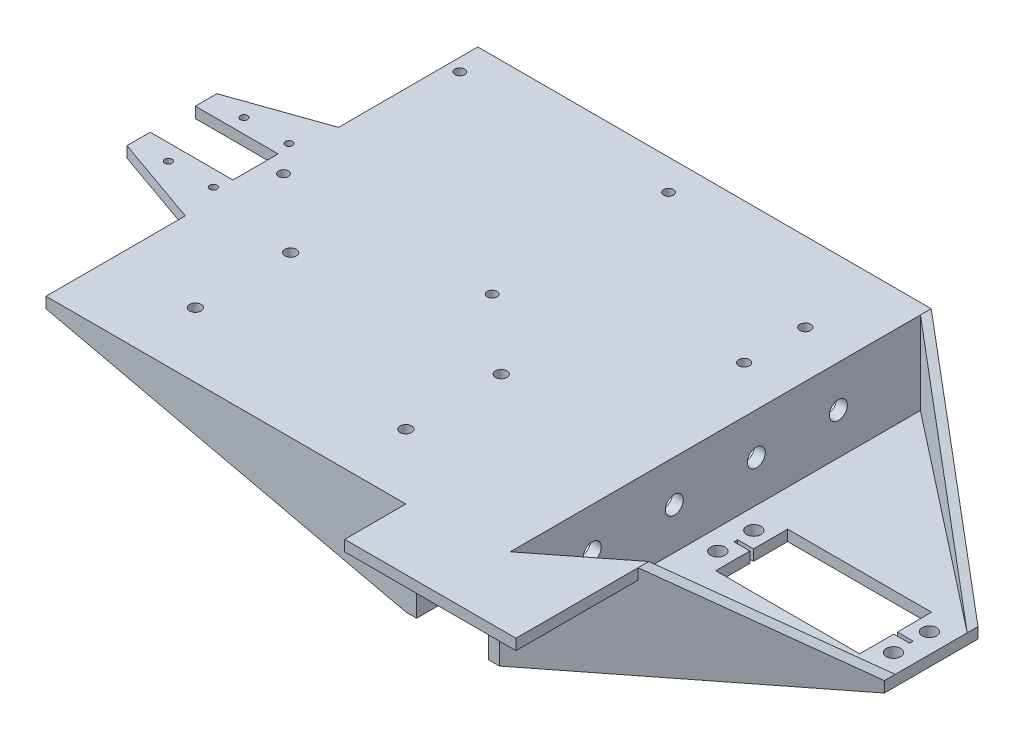
SolidWorks part; units mm, degrees
ref_plane "Front Plane" through (0, 0, 0) normal (0, 0, 1) x (1, 0, 0)
ref_plane "Top Plane" through (0, 0, 0) normal (0, 1, 0) x (1, 0, 0)
ref_plane "Right Plane" through (0, 0, 0) normal (1, 0, 0) x (0, 0, -1)
sketch "Sketch1" plane through (0, 0, 0) normal (0, 0, 1) x (1, 0, 0)
  line L0 (0, 0) -> (20, 0)
  line L1 (20, 0) -> (20, -23)
  line L2 (0, 0) -> (0, -23)
  line L3 (0, -23) -> (-103, -23)
  line L4 (-103, -23) -> (-103, -20)
  line L5 (-103, -20) -> (-3, -20)
  line L6 (-3, -20) -> (-3, 3)
  line L7 (-3, 3) -> (23, 3)
  line L8 (23, 3) -> (23, -20)
  line L9 (23, -20) -> (83, -20)
  line L10 (83, -20) -> (83, -23)
  line L11 (83, -23) -> (20, -23)
extrude "Boss-Extrude1" add sketch "Sketch1" along normal blind 120
sketch "Sketch2" plane through (0, 0, 0) normal (0, 0, -1) x (-1, 0, 0)
  line L0 (-23, 3) -> (3, 3) construction
  line L1 (-10, 3) -> (-10, 18)
  line L2 (-10, 18) -> (103, -20)
  line L3 (103, -20) -> (3, -20)
  line L4 (3, -20) -> (3, 3)
  line L5 (3, 3) -> (-10, 3)
  line L6 (-10, 18) -> (-10, 3)
  line L7 (-23, 3) -> (-23, -20)
  line L8 (-23, -20) -> (-83, -20)
  line L9 (-83, -20) -> (-10, 18)
  line L10 (-23, 3) -> (-10, 3)
  line L11 (3, 3) -> (3, 13.6283)
  line L12 (3, 13.6283) -> (-18.3982, 13.6283)
  line M4 (103, -20) -> (3, -20)
  line M5 (3, -20) -> (3, 3)
  line M6 (3, 3) -> (-23, 3)
  line M7 (-23, 3) -> (-23, -20)
  line M8 (-23, -20) -> (-83, -20)
extrude "Boss-Extrude2" add sketch "Sketch2" against normal blind 3 contours L11 L12 L1 M6 | L1 L12 L9 M8 M7 M6 | L11 L2 M5 M4
sketch "Sketch4" plane through (0, 0, 120) normal (0, 0, 1) x (1, 0, 0)
  line L0 (83, -20) -> (23, -20)
  line L1 (23, -20) -> (23, 3)
  line L2 (23, 3) -> (-3, 3)
  line L3 (-3, 3) -> (-3, -20)
  line L4 (-3, -20) -> (-103, -20) construction
  line L5 (-3, -20) -> (-3, 3) construction
  line L6 (-3, -20) -> (-103, -20)
  line L7 (-103, -20) -> (-3, 13.6283)
  line L8 (-3, 13.6283) -> (18.3982, 13.6283)
  line L9 (18.3982, 13.6283) -> (83, -20)
extrude "Boss-Extrude3" add sketch "Sketch4" against normal blind 3
sketch "Sketch5" plane through (0, -20, 0) normal (0, 1, 0) x (1, 0, 0)
  line L0 (-103, -3) -> (-103, -5)
  line L1 (-103, -117) -> (-103, -3) construction
  line L2 (-103, -5) -> (-99.5, -5)
  line L3 (-99.5, -5) -> (-99.5, -8.5)
  line L4 (-99.5, -8.5) -> (-41.5, -8.5)
  line L5 (-41.5, -8.5) -> (-41.5, -57.5)
  line L6 (-41.5, -57.5) -> (-99.5, -57.5)
  line L7 (-99.5, -57.5) -> (-99.5, -8.5)
  circle A0 centre (-99.5, -57.5) radius 1.35
  circle A1 centre (-99.5, -8.5) radius 1.35
  circle A2 centre (-41.5, -8.5) radius 1.35
  circle A3 centre (-41.5, -57.5) radius 1.35
extrude "Cut-Extrude1" cut sketch "Sketch5" against normal blind 10 contours A1 | A2 | A3 | A0
sketch "Sketch6" plane through (0, -20, 0) normal (0, 1, 0) x (1, 0, 0)
  line L0 (-103, -117) -> (-103, -3) construction
  line L1 (-103, -60) -> (-103, -40)
  line L2 (-103, -60) -> (-103, -80)
  line L3 (-103, -80) -> (-106, -80)
  line L4 (-106, -80) -> (-106, -70.5)
  line L5 (-106, -70.5) -> (-106, -49.5)
  line L6 (-106, -49.5) -> (-106, -40)
  line L7 (-106, -40) -> (-103, -40)
  line L8 (-106, -70.5) -> (-118.5, -70.5)
  line L9 (-118.5, -70.5) -> (-118.5, -49.5)
  line L10 (-118.5, -49.5) -> (-106, -49.5)
  line L11 (-108.4837, -49.5) -> (-108.4837, -53.5)
  line L12 (-108.4837, -70.5) -> (-108.4837, -66.0447)
  line L13 (-108.4837, -66.0447) -> (-103, -66.0447)
  line L14 (-103, -53.5) -> (-128, -53.5)
  line L15 (-128, -53.5) -> (-128, -49.5)
  line L16 (-128, -49.5) -> (-106, -40)
  line L17 (-108.4837, -66.0447) -> (-128, -66.0447)
  line L18 (-128, -66.0447) -> (-128, -70.5)
  line L19 (-128, -70.5) -> (-106, -80)
  line L20 (-128, -70.5) -> (-103, -81.2955)
  line L21 (-128, -49.5) -> (-103, -38.7045)
  circle A0 centre (-118.5, -49.5) radius 1
  circle A1 centre (-106, -49.5) radius 1
  circle A2 centre (-106, -70.5) radius 1
  circle A3 centre (-118.5, -70.5) radius 1
extrude "Boss-Extrude4" add sketch "Sketch6" against normal blind 3 contours A1 L6 L16 L15 L14 L9 A0 L10 | A0 L9 L14 L11 L10 | A1 L10 L11 L14 L5 | A1 L5 L14 L9 L7 L6 | L21 L7 L9 | A2 L4 L3 L2 L13 L5 | A2 L5 L13 L12 L8 | A3 L8 L12 L17 L9 | A3 L9 L17 L18 L19 L4 A2 L8 | L3 L20 L9
sketch "Sketch7" plane through (0, -23, 0) normal (0, -1, 0) x (-1, 0, 0)
  line L0 (103, -53.5) -> (105, -53.5)
  line L1 (103, -53.5) -> (128, -53.5) construction
  line L2 (105, -53.5) -> (105, -66.0447)
  line L3 (128, -66.0447) -> (103, -66.0447) construction
  line L4 (105, -66.0447) -> (103, -66.0447)
  line L5 (103, -66.0447) -> (103, -53.5) construction
  line L6 (103, -66.0447) -> (103, -53.5)
extrude "Boss-Extrude5" add sketch "Sketch7" against normal blind 3
sketch "Sketch8" plane through (0, -20, 0) normal (0, 1, 0) x (1, 0, 0)
  line L0 (-3, -117) -> (-21, -117)
  line L1 (-103, -117) -> (-3, -117) construction
  line L2 (-21, -117) -> (-21, -102)
  line L3 (-21, -102) -> (-21, -75.5)
  line L4 (-21, -75.5) -> (-79.5, -75.5)
  line L5 (-79.5, -75.5) -> (-79.5, -102)
  circle A0 centre (-79.5, -75.5) radius 1.6
  circle A1 centre (-79.5, -102) radius 1.6
  circle A2 centre (-21, -102) radius 1.6
  circle A3 centre (-21, -75.5) radius 1.6
extrude "Cut-Extrude2" cut sketch "Sketch8" against normal blind 22 contours L3 A3 L4 | L4 A3 L3 | L2 A2 L3 | L3 A2 L2 | L4 A0 L5 | L5 A0 L4 | A1
sketch "Sketch9" plane through (-3, 0, 0) normal (-1, 0, 0) x (0, 0, 1)
  line L0 (117, -20) -> (117, 3)
  line L1 (117, -8.5) -> (94.2, -8.5)
  line L2 (94.2, -8.5) -> (71.4, -8.5)
  line L3 (71.4, -8.5) -> (48.6, -8.5)
  line L4 (48.6, -8.5) -> (25.8, -8.5)
  circle A0 centre (25.8, -8.5) radius 2.5
  circle A1 centre (48.6, -8.5) radius 2.5
  circle A2 centre (71.4, -8.5) radius 2.5
  circle A3 centre (94.2, -8.5) radius 2.5
  dimension "D1" = 22.8
  dimension "D2" = 22.8
  dimension "D3" = 22.8
  dimension "D4" = 22.8
extrude "Cut-Extrude3" cut sketch "Sketch9" against normal blind 100
sketch "Sketch10" plane through (0, -20, 0) normal (0, 1, 0) x (1, 0, 0)
  line L0 (23, -60) -> (26.2, -60)
  line L1 (23, -117) -> (23, -3) construction
  line L2 (73.1, -70) -> (83.2, -70)
  line L3 (26.2, -60) -> (26.2, -55)
  line L4 (26.2, -60) -> (26.2, -65)
  line L5 (26.2, -55) -> (28.7, -55)
  line L6 (28.7, -55) -> (28.7, -65)
  line L7 (28.7, -55) -> (33.1, -55)
  line L8 (33.1, -55) -> (33.1, -65)
  line L9 (33.1, -60) -> (32.463, -60)
  line L10 (32.463, -60) -> (32.463, -59.5)
  line L11 (32.463, -60) -> (32.463, -60.5)
  line L12 (32.463, -60.5) -> (28.7, -60.5)
  line L13 (28.7, -60.5) -> (28.7, -59.5)
  line L14 (28.7, -59.5) -> (33.1, -59.5)
  line L15 (33.1, -59.5) -> (33.1, -60.5)
  line L16 (33.1, -60.5) -> (32.463, -60.5)
  line L17 (33.1, -55) -> (33.1, -50)
  line L18 (33.1, -65) -> (33.1, -70)
  line L19 (33.1, -50) -> (73.1, -50)
  line L20 (53.1, -50) -> (53.1, -70)
  line L21 (73.1, -70) -> (33.1, -70)
  line L22 (23, -70) -> (23, -50)
  line L23 (23, -50) -> (33.1, -50)
  line L24 (33.1, -70) -> (23, -70)
  line L25 (83.2, -50) -> (73.1, -50)
  line L26 (83.2, -70) -> (83.2, -50)
  line L27 (73.1, -65) -> (73.1, -70)
  line L28 (73.1, -55) -> (73.1, -50)
  line L29 (73.1, -60.5) -> (73.737, -60.5)
  line L30 (73.1, -59.5) -> (73.1, -60.5)
  line L31 (77.5, -59.5) -> (73.1, -59.5)
  line L32 (77.5, -60.5) -> (77.5, -59.5)
  line L33 (73.737, -60.5) -> (77.5, -60.5)
  line L34 (73.737, -60) -> (73.737, -60.5)
  line L35 (73.737, -60) -> (73.737, -59.5)
  line L36 (73.1, -60) -> (73.737, -60)
  line L37 (73.1, -55) -> (73.1, -65)
  line L38 (77.5, -55) -> (73.1, -55)
  line L39 (77.5, -55) -> (77.5, -65)
  line L40 (80, -55) -> (77.5, -55)
  line L41 (80, -60) -> (80, -65)
  line L42 (80, -60) -> (80, -55)
  line L43 (83.2, -60) -> (80, -60)
  circle A0 centre (28.7, -55) radius 2
  circle A1 centre (28.7, -65) radius 2
  circle A2 centre (77.5, -65) radius 2
  circle A3 centre (77.5, -55) radius 2
extrude "Cut-Extrude5" cut sketch "Sketch10" against normal blind 100
sketch "Sketch14" plane through (0, 0, 3) normal (0, 0, 1) x (1, 0, 0)
  line L0 (23, 3) -> (23, 13.6283)
  line L1 (23, 13.6283) -> (18.3982, 13.6283)
  line L2 (18.3982, 13.6283) -> (83, -20)
  line L3 (83, -20) -> (23, 13.6283)
  line M7 (83, -20) -> (18.3982, 13.6283)
extrude "Boss-Extrude8" add sketch "Sketch14" against normal blind 3 contours L3 L0 M7 | L0 L1 M7
sketch "Sketch15" plane through (0, 0, 117) normal (0, 0, -1) x (-1, 0, 0)
  line L0 (-23, 3) -> (-23, 13.6283)
  line L1 (-23, 13.6283) -> (-18.3982, 13.6283)
  line L2 (-18.3982, 13.6283) -> (-83, -20)
  line L3 (-83, -20) -> (-23, 13.6283)
  line M4 (-18.3982, 13.6283) -> (-83, -20)
extrude "Boss-Extrude9" add sketch "Sketch15" against normal blind 3 contours L3 L0 M4 | L1 L0 M4
sketch "Sketch16" plane through (0, -20, 0) normal (0, 1, 0) x (1, 0, 0)
  line L0 (23, -117) -> (83, -70)
  line L1 (83, -117) -> (83, -3) construction
  line L2 (83, -70) -> (83, -73)
  line L3 (83, -73) -> (23, -120)
  line L4 (83, -120) -> (23, -120) construction
  line L5 (23, -120) -> (23, -117)
  line L6 (23, 0) -> (23, -3)
  line L7 (23, -3) -> (83, -50)
  line L8 (83, -50) -> (83, -47)
  line L9 (83, -47) -> (23, 0)
extrude "Boss-Extrude10" add sketch "Sketch16" along normal blind 34
sketch "Sketch17" plane through (0, 0, 120) normal (0, 0, 1) x (1, 0, 0)
  line L0 (23, 13.6283) -> (23, 14)
  line L1 (23, 14) -> (83, 14)
  line L2 (23, 14) -> (83, 14) construction
  line L3 (83, 14) -> (83, -20)
  line L4 (83, -20) -> (23, 13.6283)
extrude "Cut-Extrude6" cut sketch "Sketch17" against normal blind 145
sketch "Sketch18" plane through (0, -20, 0) normal (0, 1, 0) x (1, 0, 0)
  line L0 (83, -73) -> (23, -120)
  line L1 (23, -120) -> (83, -120)
  line L2 (83, -120) -> (23, -120) construction
  line L3 (83, -120) -> (83, -73)
  line L4 (83, -47) -> (23, 0)
  line L5 (23, 0) -> (83, 0)
  line L6 (83, 0) -> (83, -47)
extrude "Cut-Extrude8" cut sketch "Sketch18" against normal blind 145 and the other way blind 145
sketch "Sketch19" plane through (0, -23, 0) normal (0, -1, 0) x (-1, 0, 0)
  line L0 (128, -49.5) -> (128, -47.5)
  line L1 (128, -47.5) -> (103, -38.7045)
  line L2 (103, -38.7045) -> (128, -49.5)
extrude "Boss-Extrude11" add sketch "Sketch19" against normal blind 3
sketch "Sketch20" plane through (0, -23, 0) normal (0, -1, 0) x (-1, 0, 0)
  line L0 (128, -70.5) -> (128, -72.5)
  line L1 (128, -72.5) -> (103, -81.2955)
  line L2 (103, -81.2955) -> (128, -70.5)
extrude "Boss-Extrude12" add sketch "Sketch20" against normal blind 3
sketch "Sketch21" plane through (0, -20, 0) normal (0, 1, 0) x (1, 0, 0)
  line L0 (73.1, -70) -> (58.1, -70)
  line L1 (73.1, -70) -> (33.1, -70) construction
  line L2 (58.1, -70) -> (58.1, -79)
  line L3 (58.1, -79) -> (62.6, -79)
  line L4 (62.6, -79) -> (62.6, -76)
  line L5 (62.6, -76) -> (53.6, -76)
  line L6 (53.6, -76) -> (53.6, -82)
  line L7 (53.6, -82) -> (62.6, -82)
  line L8 (62.6, -82) -> (62.6, -79)
extrude "Cut-Extrude9" cut sketch "Sketch21" against normal blind 10 contours L4 L5 L2 L3 | L7 L8 L3 L2 L5 L6
sketch "Sketch24" plane through (0, 3, 0) normal (0, 1, 0) x (1, 0, 0)
  line L0 (-3, -3) -> (23, -3)
  line L1 (10, -3) -> (10, -18)
  line L2 (10, -18) -> (10, -22)
  line L3 (10, -22) -> (10, -39)
  line L4 (10, -39) -> (10, -43)
  line L5 (10, -43) -> (36, -43)
  line L6 (36, -43) -> (36, -18)
  line L7 (36, -18) -> (10, -18)
  circle A0 centre (10, -39) radius 1.5
  circle A1 centre (10, -22) radius 1.5
  dimension "D1" = 15
  dimension "D2" = 4
  dimension "D3" = 17
  dimension "D4" = 4
extrude "Cut-Extrude10" cut sketch "Sketch24" against normal blind 10 contours L2 A1 L3 | L3 A1 L2 | L4 A0 L3 | L3 A0 L4
sketch "Sketch26" plane through (-3, 0, 0) normal (-1, 0, 0) x (0, 0, 1)
  line L0 (3, 3) -> (3, 0)
  line L1 (3, -20) -> (3, 3) construction
  line L2 (3, 0) -> (117, 0)
  line L3 (117, 13.6283) -> (117, -20) construction
  line L4 (117, 0) -> (117, 3)
  line L5 (117, 3) -> (3, 3)
extrude "Boss-Extrude13" add sketch "Sketch26" along normal blind 100
sketch "Sketch27" plane through (0, 3, 0) normal (0, 1, 0) x (1, 0, 0)
  line L0 (-103, -38.7045) -> (-128, -47.5)
  line L1 (-128, -47.5) -> (-128, -53.5)
  line L2 (-128, -53.5) -> (-105, -53.5)
  line L3 (-105, -53.5) -> (-105, -66.0447)
  line L4 (-105, -66.0447) -> (-128, -66.0447)
  line L5 (-128, -66.0447) -> (-128, -72.5)
  line L6 (-128, -72.5) -> (-103, -81.2955)
  line L7 (-103, -81.2955) -> (-103, -38.7045)
extrude "Boss-Extrude14" add sketch "Sketch27" against normal blind 3
sketch "Sketch29" plane through (0, 0, 0) normal (0, -1, 0) x (-1, 0, 0)
  line L0 (99.5, -8.5) -> (41.5, -8.5)
  line L1 (41.5, -8.5) -> (41.5, -57.5)
  line L2 (41.5, -57.5) -> (99.5, -57.5)
  line L3 (99.5, -57.5) -> (99.5, -8.5)
  line L4 (79.5, -75.5) -> (79.5, -102)
  line L5 (79.5, -102) -> (21, -102)
  line L6 (21, -102) -> (21, -75.5)
  line L7 (21, -75.5) -> (79.5, -75.5)
  circle A0 centre (79.5, -102) radius 1.6
  circle A1 centre (21, -102) radius 1.6
  circle A2 centre (21, -75.5) radius 1.6
  circle A3 centre (79.5, -75.5) radius 1.6
  circle A4 centre (99.5, -57.5) radius 1.35
  circle A5 centre (41.5, -57.5) radius 1.35
  circle A6 centre (41.5, -8.5) radius 1.35
  circle A7 centre (99.5, -8.5) radius 1.35
extrude "Cut-Extrude11" cut sketch "Sketch29" against normal blind 3 contours L3 A7 L0 | L0 A7 L3 | L2 A4 L3 | L3 A4 L2 | L2 A5 L1 | L1 A5 L2 | L1 A6 L0 | L0 A6 L1 | L5 A0 L4 | L4 A0 L5 | L7 A3 L4 | L4 A3 L7 | L5 A1 L6 | L6 A1 L5 | L6 A2 L7 | L7 A2 L6
sketch "Sketch30" plane through (0, 0, 0) normal (0, -1, 0) x (-1, 0, 0)
  circle A0 centre (118.5, -70.5) radius 1
  circle A1 centre (106, -70.5) radius 1
  circle A2 centre (106, -49.5) radius 1
  circle A3 centre (118.5, -49.5) radius 1
extrude "Cut-Extrude12" cut sketch "Sketch30" against normal blind 3 contours A0 | A2 | A1 | A3
sketch "Sketch31" plane through (0, 0, 120) normal (0, 0, 1) x (1, 0, 0)
  line L0 (-43.5263, 0) -> (0, 0)
  line L1 (0, 0) -> (0, -23)
  line L2 (0, -23) -> (-3, -23)
  line L3 (-103, -23) -> (0, -23) construction
  line L4 (-3, -23) -> (-3, 0)
  line L5 (-3, -23) -> (-128, -23)
  line L6 (-128, -23) -> (-128, -20)
  line L7 (-128, -20) -> (-43.5263, 0)
  line M3 (-3, 13.6283) -> (-103, -20)
  line M4 (-103, -20) -> (-103, -23)
  line M5 (-103, -23) -> (0, -23)
extrude "Cut-Extrude13" cut sketch "Sketch31" against normal blind 120 contours L4 L0 M5 M3 M4 | L7 L6 L5 M4 M3
sketch "Sketch32" plane through (0, 0, 117) normal (0, 0, 1) x (1, 0, 0)
  line L0 (-3, 0) -> (-103, 0)
  line L1 (-103, 0) -> (-103, 3)
  line L2 (-103, 3) -> (-3, 13.6283)
  line L3 (-3, 13.6283) -> (-3, 0)
extrude "Boss-Extrude15" add sketch "Sketch32" along normal blind 3
sketch "Sketch33" plane through (0, 0, 3) normal (0, 0, -1) x (-1, 0, 0)
  line L0 (3, 0) -> (3, 13.6283)
  line L1 (3, 13.6283) -> (103, 3)
  line L2 (103, 3) -> (103, 0)
  line L3 (103, 0) -> (128, 0) construction
  line L4 (103, 3) -> (103, 0) construction
  line L5 (103, 0) -> (3, 0)
extrude "Boss-Extrude16" add sketch "Sketch33" along normal blind 3
sketch "Sketch34" plane through (0, 0, 0) normal (0, 0, -1) x (-1, 0, 0)
  line L0 (103, 0) -> (3, -23)
  line L1 (3, -23) -> (3, 0)
  line L2 (3, 0) -> (103, 0)
extrude "Boss-Extrude17" add sketch "Sketch34" against normal blind 3
sketch "Sketch35" plane through (0, 0, 120) normal (0, 0, 1) x (1, 0, 0)
  line L0 (-3, -23) -> (-103, 0)
  line L1 (-103, 0) -> (-3, 0)
  line L2 (-3, 0) -> (-3, -23)
extrude "Boss-Extrude18" add sketch "Sketch35" against normal blind 3
sketch "Sketch36" plane through (0, 0, 0) normal (0, 0, -1) x (-1, 0, 0)
  line L0 (103, 3) -> (-41.9632, 3)
  line L1 (-23, 13.6283) -> (-83, -20) construction
  line L2 (-41.9632, 3) -> (-23, 13.6283)
  line L3 (-23, 13.6283) -> (3, 13.6283)
  line L4 (3, 13.6283) -> (103, 3)
  line L5 (-83, -20) -> (-23, 3)
  line L6 (-23, 13.6283) -> (-23, -23) construction
  line L7 (-23, 3) -> (-41.9632, 3)
  line L8 (-83, -20) -> (-41.9632, 3)
  line M1 (103, 3) -> (3, 13.6283)
  line M2 (3, 13.6283) -> (-23, 13.6283)
  line M3 (-23, 13.6283) -> (-23, -23)
extrude "Cut-Extrude14" cut sketch "Sketch36" against normal blind 120 contours L0 M1 M2 M3 | L2 L0 M3 | L8 L5 L0
sketch "Sketch37" plane through (0, 3, 0) normal (0, 1, 0) x (1, 0, 0)
  line L0 (23, -120) -> (44.6, -120)
  line L1 (44.6, -120) -> (44.6, -103.08)
  line L2 (83, -73) -> (23, -120) construction
  line L3 (44.6, -103.08) -> (44.6, -100.08)
  line L4 (83, -70) -> (23, -117) construction
  line L5 (44.6, -100.08) -> (23, -117)
  line L6 (23, -117) -> (23, -120)
  line L7 (23, -120) -> (44.6, -103.08)
  line M8 (23, -120) -> (23, -117)
extrude "Boss-Extrude19" add sketch "Sketch37" against normal blind 10 contours L7 L3 L5 M8
sketch "Sketch38" plane through (0, 3, 0) normal (0, 1, 0) x (1, 0, 0)
  line L0 (44.6, -100.08) -> (83, -70)
  line L1 (83, -70) -> (83, -73)
  line L2 (83, -73) -> (44.6, -103.08)
  line L3 (44.6, -103.08) -> (44.6, -100.08)
  line L19 (-128, -72.5) -> (-103, -81.2955)
  line L20 (-103, -81.2955) -> (-103, -120)
  line L21 (-103, -120) -> (23, -120)
  line L22 (23, -120) -> (44.6, -103.08)
  line L23 (44.6, -103.08) -> (44.6, -100.08)
  line L24 (44.6, -100.08) -> (23, -117)
  line L25 (23, -117) -> (23, -3)
  line L26 (23, -3) -> (23, 0)
  line L27 (23, 0) -> (-103, 0)
  line L28 (-103, 0) -> (-103, -38.7045)
  line L29 (-103, -38.7045) -> (-128, -47.5)
  line L30 (-128, -47.5) -> (-128, -53.5)
  line L31 (-128, -53.5) -> (-105, -53.5)
  line L32 (-105, -53.5) -> (-105, -66.0447)
  line L33 (-105, -66.0447) -> (-128, -66.0447)
  line L34 (-128, -66.0447) -> (-128, -72.5)
  line L35 (-128, -72.5) -> (-103, -81.2955)
  line L36 (-103, -81.2955) -> (-103, -120)
  line L37 (-103, -120) -> (23, -120)
  line L38 (23, -120) -> (44.6, -103.08)
  line L40 (44.6, -100.08) -> (23, -117)
  line L41 (23, -117) -> (23, -3)
  line L42 (23, -3) -> (23, 0)
  line L43 (23, 0) -> (-103, 0)
  line L44 (-103, 0) -> (-103, -38.7045)
  line L45 (-103, -38.7045) -> (-128, -47.5)
  line L46 (-128, -47.5) -> (-128, -53.5)
  line L47 (-128, -53.5) -> (-105, -53.5)
  line L48 (-105, -53.5) -> (-105, -66.0447)
  line L49 (-105, -66.0447) -> (-128, -66.0447)
  line L50 (-128, -66.0447) -> (-128, -72.5)
  line M28 (44.6, -103.08) -> (44.6, -100.08)
  dimension "D1" = 0
extrude "Boss-Extrude20" add sketch "Sketch38" against normal blind 23 contours L2 L1 L0 M28
sketch "Sketch39" plane through (67.0007, 0, 85.5328) normal (0.6167, 0, 0.7872) x (0.7872, 0, -0.6167)
  line L0 (-17.7848, 3) -> (20.3236, 3)
  line L1 (-55.8932, 3) -> (20.3236, 3) construction
  line L2 (20.3236, 3) -> (20.3236, -20)
  line L3 (20.3236, 3) -> (20.3236, -23) construction
  line L4 (20.3236, -20) -> (-17.7848, 3)
  line L5 (20.3236, -20) -> (22.8321, -20)
  line L6 (22.8321, -20) -> (22.8321, 3)
  line L7 (22.8321, 3) -> (20.3236, 3)
sketch "Sketch40" plane through (67.0007, 0, 85.5328) normal (0.6167, 0, 0.7872) x (0.7872, 0, -0.6167)
  line L0 (-55.8932, 3) -> (-34.2932, 3)
  line L1 (-55.8932, 3) -> (20.3236, 3) construction
  line L2 (-34.2932, 3) -> (20.3236, -20)
  line L3 (20.3236, -20) -> (20.3236, 3)
  line L4 (20.3236, 3) -> (-34.2932, 3)
  line L5 (20.3236, -20) -> (22.8321, -20)
  line L6 (22.8321, -20) -> (22.8321, 3)
  line L7 (22.8321, 3) -> (20.3236, 3)
sketch "Sketch41" plane through (0, 0, 120) normal (0, 0, 1) x (1, 0, 0)
  line L0 (23, 3) -> (44.6, 3)
  line L1 (44.6, 3) -> (83, -20)
  line L2 (83, -20) -> (84.9748, -20)
  line L3 (84.9748, -20) -> (84.9748, 3)
  line L4 (84.9748, 3) -> (44.6, 3)
extrude "Cut-Extrude15" cut sketch "Sketch41" against normal blind 69 contours L3 L4 L1 L2
sketch "Sketch42" plane through (0, 3, 0) normal (0, 1, 0) x (1, 0, 0)
  line L0 (44.6, -103.08) -> (23, -120)
  line L1 (23, -120) -> (44.6, -120)
  line L2 (44.6, -120) -> (44.6, -103.08)
  line L3 (44.6, -120) -> (44.6, -135.2)
  line L4 (44.6, -135.2) -> (-1, -135.2)
  line L5 (-1, -135.2) -> (-1, -120)
  line L6 (-103, -120) -> (23, -120) construction
  line L7 (-1, -120) -> (23, -120)
  line M6 (23, -120) -> (44.6, -103.08)
  line M21 (-103, -120) -> (23, -120)
extrude "Boss-Extrude21" add sketch "Sketch42" against normal blind 3 contours L5 L4 L3 L1 M21 | L1 L2 M6
sketch "Sketch43" plane through (0, 0, 120) normal (0, 0, 1) x (1, 0, 0)
  line L0 (-1, 0) -> (-3, 0)
  line L1 (-3, 0) -> (-3, 3)
  line L2 (-103, 3) -> (-1, 3) construction
  line L3 (-3, 3) -> (-1, 3)
  line L4 (-1, 3) -> (-1, 0)
extrude "Boss-Extrude22" add sketch "Sketch43" along normal blind 17 contours L4 L0 L1 L3
sketch "Sketch44" plane through (0, 0, 135.2) normal (0, 0, 1) x (1, 0, 0)
  line L1 (-1, 0) -> (44.6, 0)
  line L2 (-1, 0) -> (-1, 3)
  line L3 (-1, 3) -> (44.6, 3)
  line L4 (44.6, 0) -> (44.6, 3)
extrude "Boss-Extrude23" add sketch "Sketch44" along normal blind 1.8
